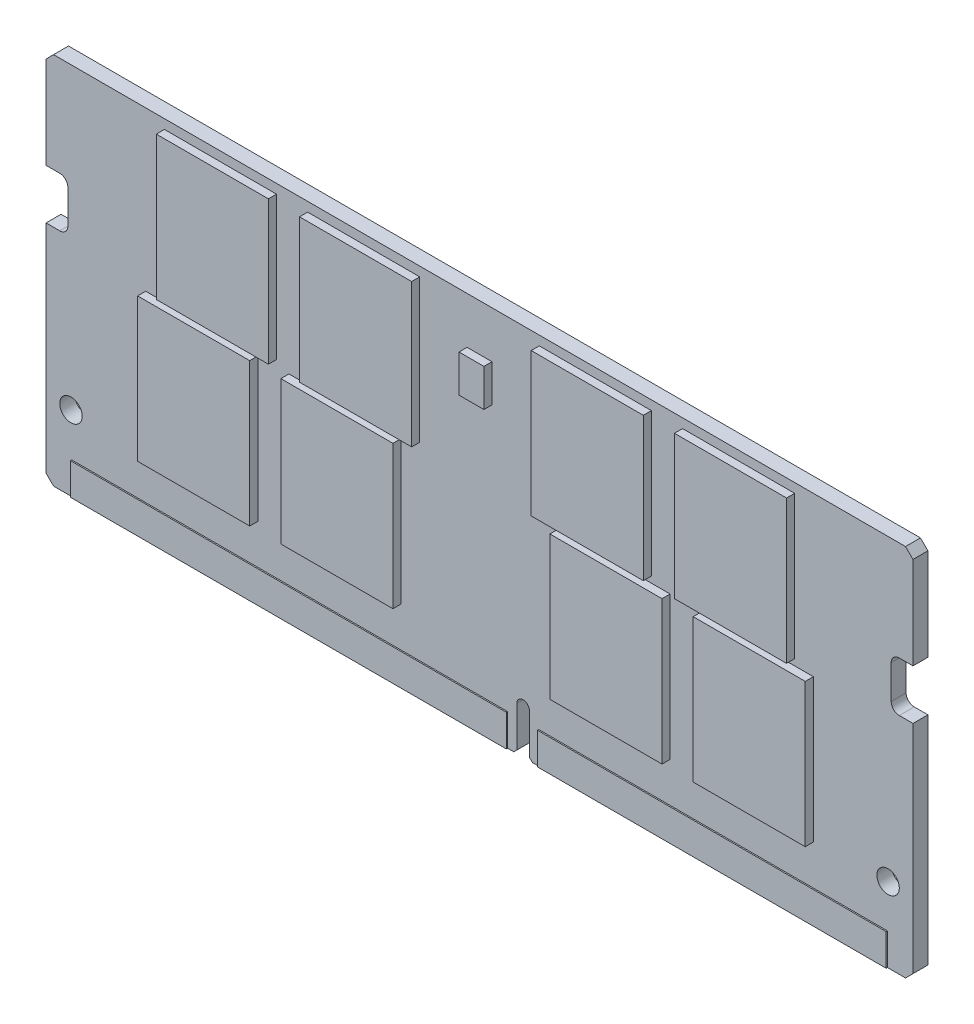
SolidWorks part; units mm, degrees
ref_plane "Front Plane" through (0, 0, 0) normal (0, 0, 1) x (1, 0, 0)
ref_plane "Top Plane" through (0, 0, 0) normal (0, 1, 0) x (1, 0, 0)
ref_plane "Right Plane" through (0, 0, 0) normal (1, 0, 0) x (0, 0, -1)
sketch "Sketch1" plane through (0, 0, 0) normal (0, 0, 1) x (1, 0, 0)
  line L0 (-34.2, 15) -> (-34.8, 14.4)
  line L1 (34.2, -15) -> (-34.2, -15)
  line L2 (34.8, -14.4) -> (34.8, 14.4)
  line L3 (34.2, 15) -> (-34.2, 15)
  line L4 (-34.8, -14.4) -> (-34.8, 14.4)
  line L5 (34.8, -15) -> (-34.8, 15) construction
  line L6 (34.8, 15) -> (-34.8, -15) construction
  line L7 (-34.2, -15) -> (-34.8, -14.4)
  line L8 (34.8, 14.4) -> (34.2, 15)
  line L9 (34.8, -14.4) -> (34.2, -15)
  point P0 (0, 0)
  dimension "D1" = 69.6
  dimension "D2" = 30
extrude "Main Board" add sketch "Sketch1" along normal blind 1.2
sketch "Sketch2" plane through (0, 0, 1.2) normal (0, 0, 1) x (1, 0, 0)
  line L0 (-34.8, 14.4) -> (-34.8, -14.4) construction
  line L1 (-36.55, 3) -> (-33.7, 3)
  line L2 (-36.55, 3) -> (-36.55, 7)
  line L3 (-36.55, 7) -> (-33.7, 7)
  line L4 (-33.05, 3.65) -> (-33.05, 6.35)
  line L5 (-36.55, 3) -> (-33.05, 7) construction
  line L6 (-36.55, 7) -> (-33.05, 3) construction
  line L7 (-34.2, -15) -> (34.2, -15) construction
  line L8 (0, 0) -> (0, -17.1346) construction
  line L9 (36.55, 7) -> (33.05, 3) construction
  line L10 (36.55, 3) -> (33.05, 7) construction
  line L11 (33.05, 3.65) -> (33.05, 6.35)
  line L12 (36.55, 7) -> (33.7, 7)
  line L13 (36.55, 3) -> (36.55, 7)
  line L14 (36.55, 3) -> (33.7, 3)
  line L15 (3.5, -15) -> (3.5, -11.5) construction
  line L16 (3, -15) -> (3, -11.5)
  line L17 (4, -15) -> (4, -11.5)
  line L18 (-34.8, 14.4) -> (-34.8, -14.4) construction
  line L19 (-34.2, -15) -> (34.2, -15) construction
  arc A0 (-33.7, 3) -> (-33.05, 3.65) centre (-33.7, 3.65) ccw
  arc A1 (-33.7, 7) -> (-33.05, 6.35) centre (-33.7, 6.35) cw
  arc A2 (33.7, 7) -> (33.05, 6.35) centre (33.7, 6.35) ccw
  arc A3 (33.7, 3) -> (33.05, 3.65) centre (33.7, 3.65) cw
  circle A4 centre (-32.8, -9) radius 0.9
  circle A5 centre (32.8, -9) radius 0.9
  arc A6 (3, -15) -> (4, -15) centre (3.5, -15) ccw
  arc A7 (4, -11.5) -> (3, -11.5) centre (3.5, -11.5) ccw
  point P0 (-34.8, 5)
  point P28 (34.8, 5)
  point P35 (3.5, -13.25)
  dimension "D4" = 0.65
  dimension "D5" = 1.8
  dimension "D8" = 1
  dimension "D1" = 1.75
  dimension "D2" = 20
  dimension "D3" = 4
  dimension "D6" = 2
  dimension "D7" = 6
  dimension "D9" = 38.3
  dimension "D10" = 4
extrude "Detail Cuts" cut sketch "Sketch2" against normal blind 1.2
chamfer "Chamfer1" distance 0.25 angle 45 2 edges at (4, -15, 0.6) (3, -15, 0.6)
sketch "Sketch3" plane through (0, 0, 0) normal (0, 0, -1) x (-1, 0, 0)
  line L0 (33.9604, 38.7472) -> (327.2937, 38.7472) construction
  line L1 (-34.2, 15) -> (34.2, 15) construction
  line L2 (-25.3, 14.25) -> (-16.3, 14.25)
  line L3 (-25.3, 14.25) -> (-25.3, 2.75)
  line L4 (-25.3, 2.75) -> (-16.3, 2.75)
  line L5 (-16.3, 14.25) -> (-16.3, 2.75)
  line L6 (-13.8, 14.25) -> (-4.8, 14.25)
  line L7 (-13.8, 14.25) -> (-13.8, 2.75)
  line L8 (-13.8, 2.75) -> (-4.8, 2.75)
  line L9 (-4.8, 14.25) -> (-4.8, 2.75)
  line L10 (-34.8, 7) -> (-34.8, 14.4) construction
  line L11 (0, 0) -> (0, 1.0643) construction
  line L12 (6.3, -9.25) -> (6.3, 2.25)
  line L13 (-26.8, -9.25) -> (-17.8, -9.25)
  line L14 (-26.8, -9.25) -> (-26.8, 2.25)
  line L15 (-26.8, 2.25) -> (-17.8, 2.25)
  line L16 (-17.8, -9.25) -> (-17.8, 2.25)
  line L17 (-15.3, -9.25) -> (-6.3, -9.25)
  line L18 (-15.3, -9.25) -> (-15.3, 2.25)
  line L19 (-15.3, 2.25) -> (-6.3, 2.25)
  line L20 (-6.3, -9.25) -> (-6.3, 2.25)
  line L21 (15.3, 2.25) -> (6.3, 2.25)
  line L22 (15.3, -9.25) -> (15.3, 2.25)
  line L23 (15.3, -9.25) -> (6.3, -9.25)
  line L24 (17.8, -9.25) -> (17.8, 2.25)
  line L25 (26.8, 2.25) -> (17.8, 2.25)
  line L26 (26.8, -9.25) -> (26.8, 2.25)
  line L27 (26.8, -9.25) -> (17.8, -9.25)
  line L28 (4.8, 14.25) -> (4.8, 2.75)
  line L29 (13.8, 2.75) -> (4.8, 2.75)
  line L30 (13.8, 14.25) -> (13.8, 2.75)
  line L31 (13.8, 14.25) -> (4.8, 14.25)
  line L32 (16.3, 14.25) -> (16.3, 2.75)
  line L33 (25.3, 2.75) -> (16.3, 2.75)
  line L34 (25.3, 14.25) -> (25.3, 2.75)
  line L35 (25.3, 14.25) -> (16.3, 14.25)
  dimension "D1" = 11.5
  dimension "D2" = 9
  dimension "D3" = 0.75
  dimension "D4" = 9.5
  dimension "D5" = 2.5
  dimension "D6" = 9
  dimension "D7" = 11.5
  dimension "D8" = 9
  dimension "D9" = 0.5
  dimension "D10" = 1.5
  dimension "D11" = 2.5
  dimension "D12" = 9
extrude "SOC1" add sketch "Sketch3" along normal blind 0.65 and the other way offset from surface (1.85 mm away) 0.65 other way up to face at (31.9, -9, 1.2)
sketch "Sketch4" plane through (0, 0, 1.2) normal (0, 0, 1) x (1, 0, 0)
  line L0 (32.2744, 70.6245) -> (306.941, 70.6245) construction
  line L1 (0, 8.25) -> (0, 0) construction
  line L2 (-1, 11.25) -> (1, 11.25)
  line L3 (-1, 11.25) -> (-1, 8.25)
  line L4 (-1, 8.25) -> (1, 8.25)
  line L5 (1, 11.25) -> (1, 8.25)
  dimension "D1" = 2
  dimension "D2" = 8.25
  dimension "D3" = 3
extrude "SOC2" add sketch "Sketch4" along normal blind 0.65
sketch "Sketch5" plane through (0, 0, 1.2) normal (0, 0, 1) x (1, 0, 0)
  line L0 (-34.2, -15) -> (2.75, -15) construction
  line L1 (-32.75, -15) -> (2.25, -15)
  line L2 (-32.75, -15) -> (-32.75, -12.45)
  line L3 (-32.75, -12.45) -> (2.25, -12.45)
  line L4 (2.25, -15) -> (2.25, -12.45)
  line L5 (3, -11.5) -> (3, -14.75) construction
  line L6 (4.25, -15) -> (34.2, -15) construction
  line L7 (4.75, -15) -> (32.75, -15)
  line L8 (4.75, -15) -> (4.75, -12.45)
  line L9 (4.75, -12.45) -> (32.75, -12.45)
  line L10 (32.75, -15) -> (32.75, -12.45)
  line L11 (4, -14.75) -> (4, -11.5) construction
  dimension "D1" = 2.55
  dimension "D2" = 35
  dimension "D3" = 0.75
  dimension "D4" = 0.75
  dimension "D5" = 28
extrude "Contacts" add sketch "Sketch5" along normal blind 0.1 and the other way offset from surface (1.3 mm away) 0.1 other way up to face at (-20.8, 8.5, 0)
